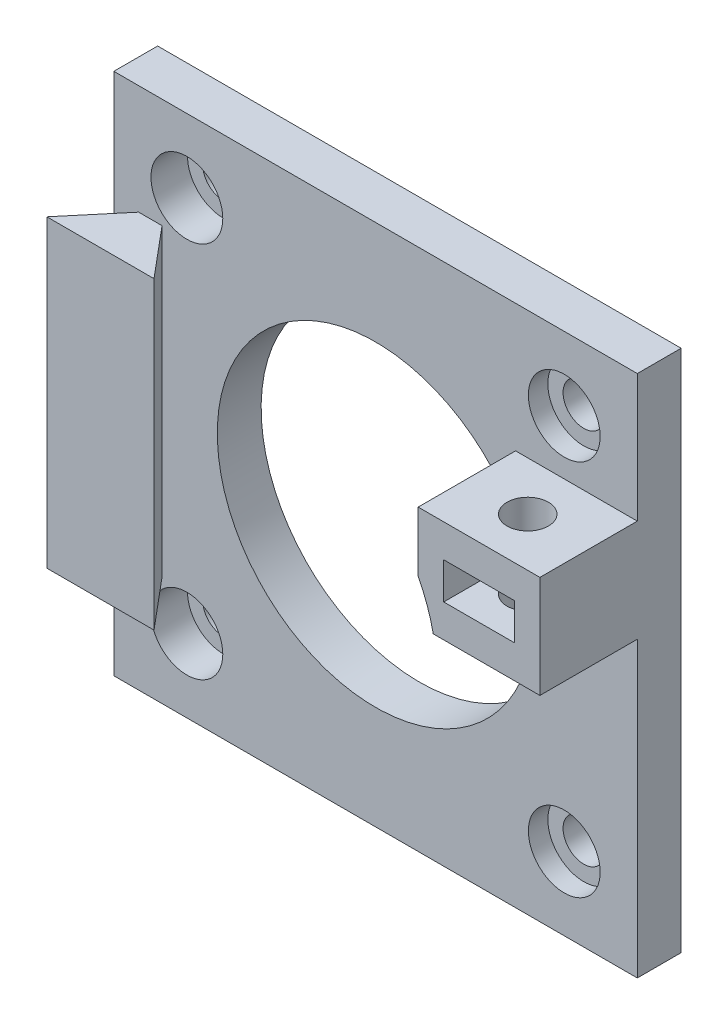
SolidWorks part; units mm, degrees
ref_plane "Alzado" through (0, 0, 0) normal (0, 0, 1) x (1, 0, 0)
ref_plane "Planta" through (0, 0, 0) normal (0, 1, 0) x (1, 0, 0)
ref_plane "Vista lateral" through (0, 0, 0) normal (1, 0, 0) x (0, 0, -1)
sketch "Croquis1" plane through (0, 0, 0) normal (0, 0, 1) x (1, 0, 0)
  line L1 (21.5, -21.5) -> (-21.5, -21.5)
  line L2 (21.5, -21.5) -> (21.5, 21.5)
  line L3 (21.5, 21.5) -> (-21.5, 21.5)
  line L4 (-21.5, -21.5) -> (-21.5, 21.5)
  line L5 (21.5, -21.5) -> (-21.5, 21.5) construction
  line L6 (21.5, 21.5) -> (-21.5, -21.5) construction
  line L7 (15.5, -15.5) -> (-15.5, -15.5) construction
  line L8 (15.5, -15.5) -> (15.5, 15.5) construction
  line L9 (15.5, 15.5) -> (-15.5, 15.5) construction
  line L10 (-15.5, -15.5) -> (-15.5, 15.5) construction
  line L11 (15.5, -15.5) -> (-15.5, 15.5) construction
  line L12 (15.5, 15.5) -> (-15.5, -15.5) construction
  circle A0 centre (0, 0) radius 13
  circle A1 centre (-15.5, 15.5) radius 1.7
  circle A2 centre (-15.5, -15.5) radius 1.7
  circle A3 centre (15.5, -15.5) radius 1.7
  circle A4 centre (15.5, 15.5) radius 1.7
  point P0 (0, 0)
  point P6 (0, 0)
  dimension "D3" = 26
  dimension "D4" = 3.4
  dimension "D1" = 43
  dimension "D2" = 31
extrude "Saliente-Extruir1" add sketch "Croquis1" along normal blind 3.6
sketch "Croquis2" plane through (0, 0, 3.6) normal (0, 0, 1) x (1, 0, 0)
  circle A0 centre (-15.5, 15.5) radius 2.95
  circle A1 centre (15.5, 15.5) radius 2.95
  circle A2 centre (-15.5, -15.5) radius 2.95
  circle A3 centre (15.5, -15.5) radius 2.95
  dimension "D1" = 5.9
extrude "Cortar-Extruir1" cut sketch "Croquis2" against normal blind 1.6
sketch "Croquis3" plane through (0, 0, 3.6) normal (0, 0, 1) x (1, 0, 0)
  line L0 (21.5, -21.5) -> (21.5, 21.5) construction
  line L1 (21.5, 2.6) -> (12.7373, 2.6)
  line L2 (21.5, 2.6) -> (21.5, 11)
  line L3 (21.5, 11) -> (11.5, 11)
  line L4 (11.5, 6.0622) -> (11.5, 11)
  arc A0 (12.7373, 2.6) -> (11.5, 6.0622) centre (0, 0) ccw
  circle A1 centre (0, 0) radius 13 construction
  dimension "D1" = 11.5
  dimension "D2" = 11
  dimension "D3" = 8.4
extrude "Saliente-Extruir2" add sketch "Croquis3" along normal blind 8
sketch "Croquis4" plane through (0, 2.6, 0) normal (0, -1, 0) x (1, 0, 0)
  line L0 (12.7373, 3.6) -> (21.5, 3.6) construction
  line L1 (21.5, 11.6) -> (21.5, 3.6) construction
  circle A0 centre (16.5, 7.6) radius 1.7
  dimension "D3" = 3.4
  dimension "D1" = 4
  dimension "D2" = 5
extrude "Cortar-Extruir2" cut sketch "Croquis4" against normal blind 10
ref_plane "Plano1" through (0, 6.8, 0) normal (0, -1, 0) x (-1, 0, 0)
sketch "Croquis6" plane through (0, 6.8, 0) normal (0, -1, 0) x (-1, 0, 0)
  line L0 (-13.5988, -9.275) -> (-13.5988, -15.925)
  line L1 (-16.5, -10.95) -> (-13.5988, -9.275) construction
  line L2 (-13.5988, -9.275) -> (-13.5988, -5.925)
  line L3 (-13.5988, -5.925) -> (-16.5, -4.25)
  line L4 (-16.5, -4.25) -> (-19.4012, -5.925)
  line L5 (-19.4012, -5.925) -> (-19.4012, -9.275)
  line L6 (-19.4012, -9.275) -> (-16.5, -10.95) construction
  line L7 (-13.5988, -15.925) -> (-19.4012, -15.925)
  line L8 (-19.4012, -15.925) -> (-19.4012, -9.275)
  line L9 (-12.7373, -11.6) -> (-12.7373, -3.6) construction
  circle A0 centre (-16.5, -7.6) radius 3.35 construction
  dimension "D1" = 6.7
  dimension "D2" = 10
extrude "Cortar-Extruir3" cut sketch "Croquis6" against normal blind 1.5 and the other way blind 1.5
sketch "Croquis7" plane through (0, 0, 0) normal (0, 1, 0) x (1, 0, 0)
  line L0 (-22.9, -7.7) -> (-18.5, -2.4563)
  line L1 (-18.5, -2.4563) -> (-14.1, -7.7)
  line L2 (-14.1, -7.7) -> (-22.9, -7.7)
  line L3 (-21.5, -3.6) -> (21.5, -3.6) construction
  dimension "D1" = 18.5
  dimension "D2" = 4.1
  dimension "D3" = 8.8
  dimension "D4" = 50
  dimension "D5" = 50
extrude "Saliente-Extruir3" add sketch "Croquis7" along normal blind 12.5 and the other way blind 12.5
sketch "Croquis8" plane through (0, 0, 3.6) normal (0, 0, 1) x (1, 0, 0)
  circle A0 centre (-15.5, -15.5) radius 2.95 construction
  circle A1 centre (-15.5, 15.5) radius 2.95 construction
  circle A2 centre (-15.5, -15.5) radius 2.95
  circle A3 centre (-15.5, 15.5) radius 2.95
extrude "Cortar-Extruir4" cut sketch "Croquis8" against normal blind 3
